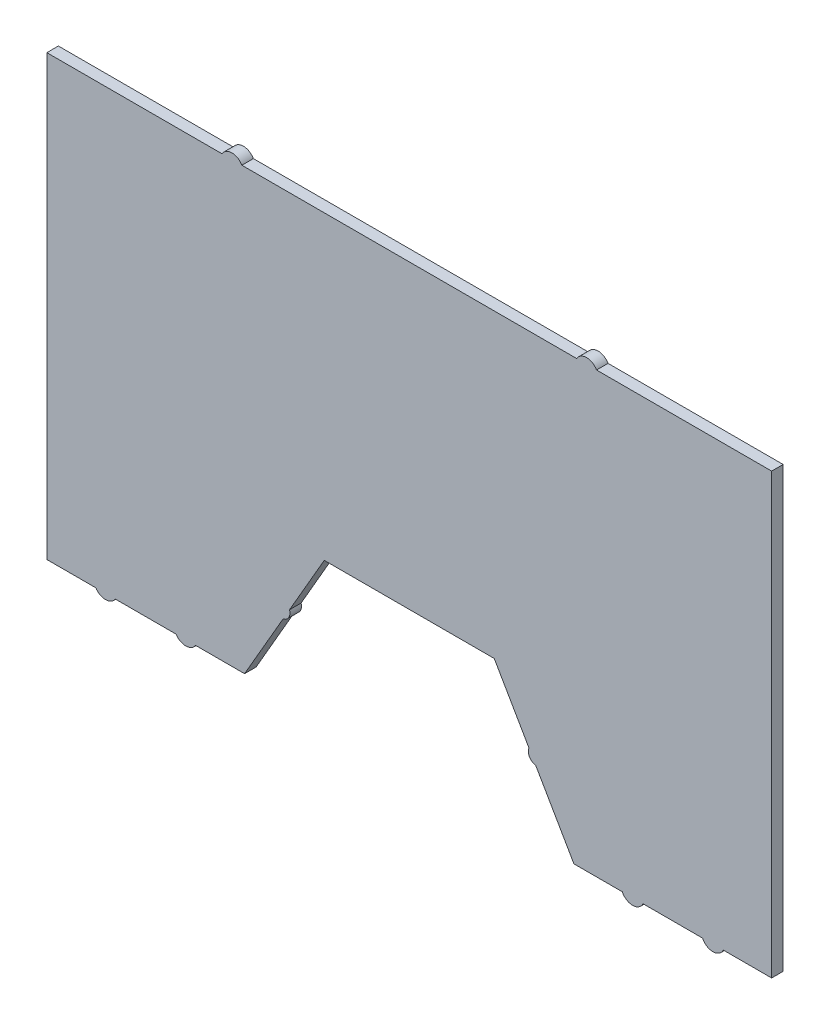
SolidWorks part; units mm, degrees
ref_plane "Front Plane" through (0, 0, 0) normal (0, 0, 1) x (1, 0, 0)
ref_plane "Top Plane" through (0, 0, 0) normal (0, 1, 0) x (1, 0, 0)
ref_plane "Right Plane" through (0, 0, 0) normal (1, 0, 0) x (0, 0, -1)
sketch "Sketch1" plane through (0, 0, 0) normal (0, 0, 1) x (1, 0, 0)
  line L40 (-114.9834, -41.5953) -> (-88.5527, -41.5953)
  line L41 (-80.0924, -41.5953) -> (-58.7882, -41.5953)
  line L42 (-58.7882, -41.5953) -> (-42.0428, -12.5915)
  line L43 (-39.2477, -7.7503) -> (-24.1471, 18.4047)
  line L44 (-24.1471, 18.4047) -> (49.7537, 18.4047)
  line L45 (49.7537, 18.4047) -> (64.8431, -7.7309)
  line L46 (67.7903, -12.8357) -> (84.3947, -41.5953)
  line L47 (84.3947, -41.5953) -> (105.4082, -41.5953)
  line L48 (114.4484, -41.5953) -> (140.3009, -41.5953)
  line L49 (149.3411, -41.5953) -> (170.3546, -41.5953)
  line L50 (170.3546, -41.5953) -> (170.3546, 149.2581)
  line L51 (170.3546, 149.2581) -> (94.2344, 149.2581)
  line L52 (85.5742, 149.2581) -> (-59.9675, 149.2581)
  line L53 (-68.6278, 149.2581) -> (-144.748, 149.2581)
  line L54 (-144.748, 149.2581) -> (-144.748, -41.5953)
  line L55 (-144.748, -41.5953) -> (-123.4438, -41.5953)
  line L56 (-114.9834, -41.5953) -> (-88.5527, -41.5953)
  line L57 (-80.0924, -41.5953) -> (-58.7882, -41.5953)
  line L58 (-58.7882, -41.5953) -> (-42.0428, -12.5915)
  line L59 (-39.2477, -7.7503) -> (-24.1471, 18.4047)
  line L60 (-24.1471, 18.4047) -> (49.7537, 18.4047)
  line L61 (49.7537, 18.4047) -> (64.8431, -7.7309)
  line L62 (67.7903, -12.8357) -> (84.3947, -41.5953)
  line L63 (84.3947, -41.5953) -> (105.4082, -41.5953)
  line L64 (114.4484, -41.5953) -> (140.3009, -41.5953)
  line L65 (149.3411, -41.5953) -> (170.3546, -41.5953)
  line L66 (170.3546, -41.5953) -> (170.3546, 149.2581)
  line L67 (170.3546, 149.2581) -> (94.2344, 149.2581)
  line L68 (85.5742, 149.2581) -> (-59.9675, 149.2581)
  line L69 (-68.6278, 149.2581) -> (-144.748, 149.2581)
  line L70 (-144.748, 149.2581) -> (-144.748, -41.5953)
  line L71 (-144.748, -41.5953) -> (-123.4438, -41.5953)
  arc A12 (-123.4438, -41.5953) -> (-114.9834, -41.5953) centre (-119.2136, -38.9297) ccw
  arc A13 (-88.5527, -41.5953) -> (-80.0924, -41.5953) centre (-84.3226, -38.9297) ccw
  arc A14 (-42.0428, -12.5915) -> (-39.2477, -7.7503) centre (-42.8103, -8.9209) ccw
  arc A15 (64.8431, -7.7309) -> (67.7903, -12.8357) centre (68.3248, -9.1239) ccw
  arc A16 (105.4082, -41.5953) -> (114.4484, -41.5953) centre (109.9283, -39.4579) ccw
  arc A17 (140.3009, -41.5953) -> (149.3411, -41.5953) centre (144.821, -39.4579) ccw
  arc A18 (94.2344, 149.2581) -> (85.5742, 149.2581) centre (89.9043, 146.7581) ccw
  arc A19 (-59.9675, 149.2581) -> (-68.6278, 149.2581) centre (-64.2976, 146.7581) ccw
  arc A20 (-123.4438, -41.5953) -> (-114.9834, -41.5953) centre (-119.2136, -38.9297) ccw
  arc A21 (-88.5527, -41.5953) -> (-80.0924, -41.5953) centre (-84.3226, -38.9297) ccw
  arc A22 (-42.0428, -12.5915) -> (-39.2477, -7.7503) centre (-42.8103, -8.9209) ccw
  arc A23 (64.8431, -7.7309) -> (67.7903, -12.8357) centre (68.3248, -9.1239) ccw
  arc A24 (105.4082, -41.5953) -> (114.4484, -41.5953) centre (109.9283, -39.4579) ccw
  arc A25 (140.3009, -41.5953) -> (149.3411, -41.5953) centre (144.821, -39.4579) ccw
  arc A26 (94.2344, 149.2581) -> (85.5742, 149.2581) centre (89.9043, 146.7581) ccw
  arc A27 (-59.9675, 149.2581) -> (-68.6278, 149.2581) centre (-64.2976, 146.7581) ccw
  dimension "D1" = 0
extrude "Boss-Extrude1" add sketch "Sketch1" along normal blind 5
